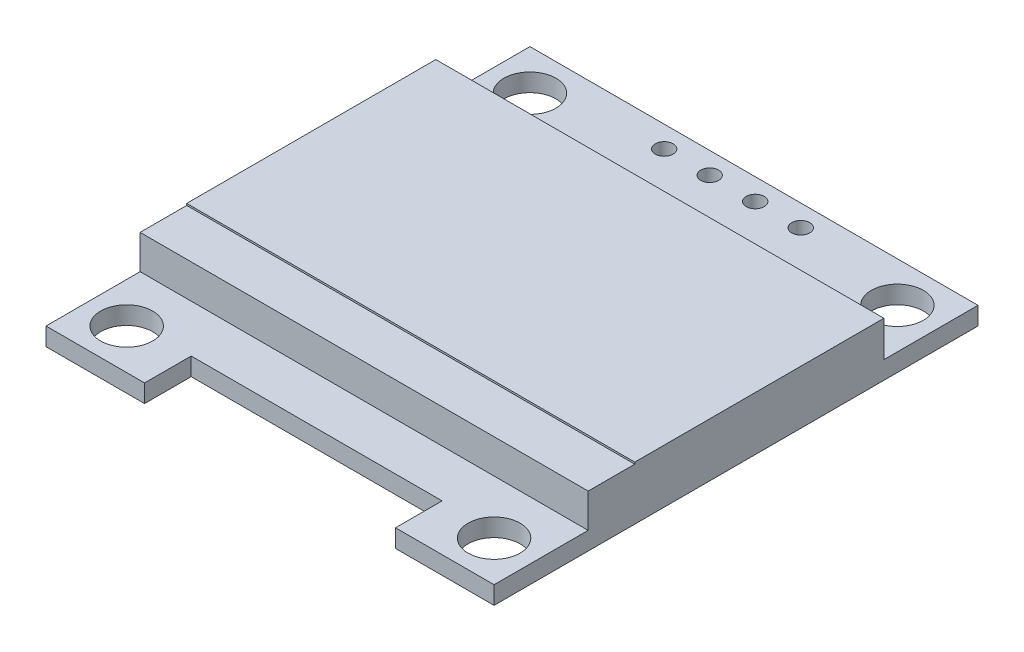
SolidWorks part; units mm, degrees
ref_plane "前视基准面" through (0, 0, 0) normal (0, 0, 1) x (1, 0, 0)
ref_plane "上视基准面" through (0, 0, 0) normal (0, 1, 0) x (1, 0, 0)
ref_plane "右视基准面" through (0, 0, 0) normal (1, 0, 0) x (0, 0, -1)
sketch "草图1" plane through (0, 0, 0) normal (0, 1, 0) x (1, 0, 0)
  line L1 (-12.5, 13.5) -> (12.5, 13.5)
  line L2 (-12.5, 13.5) -> (-12.5, -13.5)
  line L3 (-12.5, -13.5) -> (12.5, -13.5)
  line L4 (12.5, 13.5) -> (12.5, -13.5)
  line L5 (-12.5, 13.5) -> (12.5, -13.5) construction
  line L6 (-12.5, -13.5) -> (12.5, 13.5) construction
  point P0 (0, 0)
  dimension "D1" = 27
  dimension "D2" = 25
extrude "凸台-拉伸1" add sketch "草图1" along normal blind 1
sketch "草图2" plane through (0, 1, 0) normal (0, 1, 0) x (1, 0, 0)
  line L0 (-12.5, 13.5) -> (-12.5, -13.5) construction
  line L5 (-12.5, 8.25) -> (12.5, 8.25)
  line L6 (-12.5, 8.25) -> (-12.5, -8.25)
  line L7 (-12.5, -8.25) -> (12.5, -8.25)
  line L8 (12.5, 8.25) -> (12.5, -8.25)
  line L9 (12.5, -13.5) -> (12.5, 13.5) construction
  line L12 (0, 0) -> (12.5, 0) construction
  point P10 (0, 0)
  point P11 (0, 0)
  point P13 (0, 0)
  dimension "D1" = 16.5
extrude "凸台-拉伸2" add sketch "草图2" along normal blind 2.9 from surface at -1 starting at face at (0, 0, 0)
sketch "草图3" plane through (0, 2.9, 0) normal (0, 1, 0) x (1, 0, 0)
  line L0 (12.5, -8.25) -> (12.5, 8.25) construction
  line L1 (-12.5, 8.25) -> (12.5, 8.25)
  line L2 (-12.5, 8.25) -> (-12.5, -5.65)
  line L3 (-12.5, -5.65) -> (12.5, -5.65)
  line L4 (12.5, 8.25) -> (12.5, -5.65)
  dimension "D1" = 13.9
extrude "凸台-拉伸3" add sketch "草图3" along normal blind 3 from surface at -2.9 starting at face at (0, 0, 0)
sketch "草图4" plane through (0, 1, 0) normal (0, 1, 0) x (1, 0, 0)
  line L0 (-12.5, -13.5) -> (12.5, -13.5) construction
  line L1 (-7, -10.9) -> (7, -10.9)
  line L2 (-7, -10.9) -> (-7, -13.5)
  line L3 (-7, -13.5) -> (7, -13.5)
  line L4 (7, -10.9) -> (7, -13.5)
  line L5 (0, 0) -> (0, -13.5) construction
  dimension "D1" = 2.6
  dimension "D2" = 14
extrude "切除-拉伸1" cut sketch "草图4" against normal through all
sketch "草图6" plane through (0, 1, 0) normal (0, 1, 0) x (1, 0, 0)
  line L0 (-10.25, 13.5) -> (-10.25, 12.7) construction
  line L1 (12.5, 13.5) -> (-12.5, 13.5) construction
  line L2 (-11.7, 11.25) -> (-12.5, 11.25) construction
  line L3 (-12.5, 13.5) -> (-12.5, 8.25) construction
  line L4 (0, 13.5) -> (0, 0) construction
  line L5 (0, 0) -> (-12.5, 0) construction
  line L6 (-12.5, 8.25) -> (-12.5, -5.65) construction
  line L7 (11.7, 11.25) -> (12.5, 11.25) construction
  line L8 (10.25, 13.5) -> (10.25, 12.7) construction
  circle A0 centre (-10.25, 11.25) radius 1.45
  circle A1 centre (10.25, 11.25) radius 1.45
  circle A2 centre (-10.25, -11.25) radius 1.45
  circle A3 centre (10.25, -11.25) radius 1.45
  circle A4 centre (-3.81, 12.3) radius 0.5
  circle A5 centre (-1.27, 12.3) radius 0.5
  circle A6 centre (1.27, 12.3) radius 0.5
  circle A7 centre (3.81, 12.3) radius 0.5
  point P28 (0, 0)
  dimension "D1" = 2.9
  dimension "D3" = 1
  dimension "D2" = 0.8
  dimension "D4" = 1.2
  dimension "D5" = 4
extrude "切除-拉伸2" cut sketch "草图6" against normal through all
sketch "草图7" plane through (0, 0, 0) normal (0, -1, 0) x (1, 0, 0)
  line L1 (-3.8831, -2.6923) -> (-3.2618, -2.6923)
  line L2 (-3.8831, -2.6923) -> (-3.8831, -4.8151)
  line L3 (-3.8831, -4.8151) -> (-3.2618, -4.8151)
  line L4 (-3.2618, -2.6923) -> (-3.2618, -4.8151)
extrude "凸台-拉伸4" add sketch "草图7" along normal blind 4 from surface at -3 starting at face at (0, 3, -1.3)
